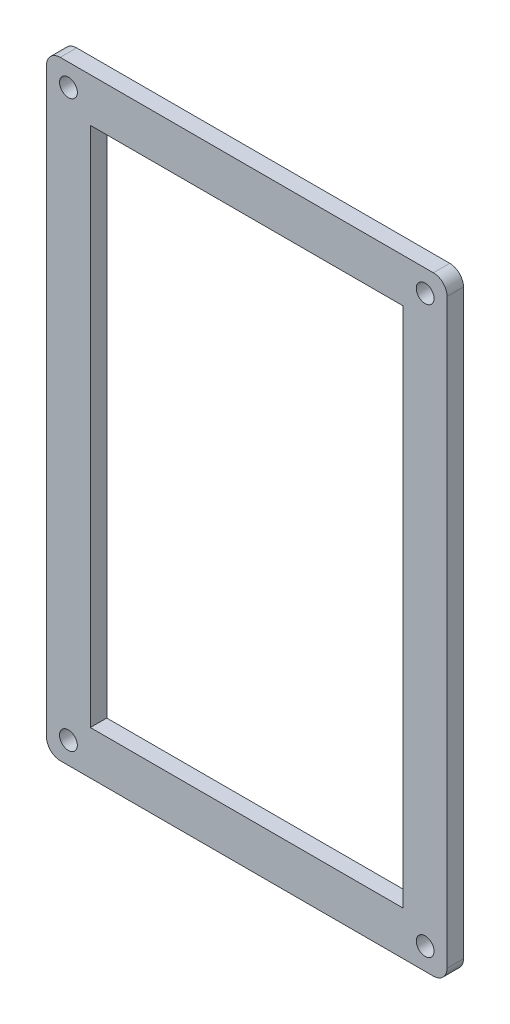
SolidWorks part; units mm, degrees
material "有机玻璃 (TM) GS 丙烯酸铸钣"
ref_plane "前视基准面" through (0, 0, 0) normal (0, 0, 1) x (1, 0, 0)
ref_plane "上视基准面" through (0, 0, 0) normal (0, 1, 0) x (1, 0, 0)
ref_plane "右视基准面" through (0, 0, 0) normal (1, 0, 0) x (0, 0, -1)
sketch "Model" plane through (0, 0, 0) normal (0, 0, 1) x (1, 0, 0)
  line L0 (73.1731, 8.0112) -> (73.1731, 108.761)
  line L1 (8.0228, 111.261) -> (70.6731, 111.261)
  line L2 (65.1731, 0.0112) -> (2.5228, 0.0112)
  line L3 (0.0228, 8.0112) -> (0.0228, 108.761)
  line L4 (8.0228, 111.261) -> (2.5228, 111.261)
  line L5 (0.0228, 8.0112) -> (0.0228, 2.5112)
  line L6 (65.1731, 0.0112) -> (70.6731, 0.0112)
  line L7 (73.1731, 8.0112) -> (73.1731, 2.5112)
  line L8 (8.0228, 103.261) -> (65.1731, 103.261)
  line L9 (8.0228, 103.261) -> (8.0228, 8.0112)
  line L10 (65.1731, 103.261) -> (65.1731, 8.0112)
  line L11 (65.1731, 8.0112) -> (8.0228, 8.0112)
  line L12 (8.0228, 0.0112) -> (8.0228, -3.6091)
  arc A0 (0.0228, 2.5112) -> (2.5228, 0.0112) centre (2.5228, 2.5112) ccw
  arc A1 (70.6731, 0.0112) -> (73.1731, 2.5112) centre (70.6731, 2.5112) ccw
  arc A2 (73.1731, 108.761) -> (70.6731, 111.261) centre (70.6731, 108.761) ccw
  arc A3 (2.5228, 111.261) -> (0.0228, 108.761) centre (2.5228, 108.761) ccw
  circle A4 centre (69.1731, 107.261) radius 1.625
  circle A5 centre (4.0228, 107.261) radius 1.625
  circle A6 centre (4.0228, 4.0112) radius 1.625
  circle A7 centre (69.1731, 4.0112) radius 1.625
extrude "凸台-拉伸1" add sketch "Model" along normal blind 3 contours L4 A3 L3 L5 A0 L2 L6 A1 L7 L0 A2 L1 A7 A6 A5 A4 L10 L11 L9 L8
